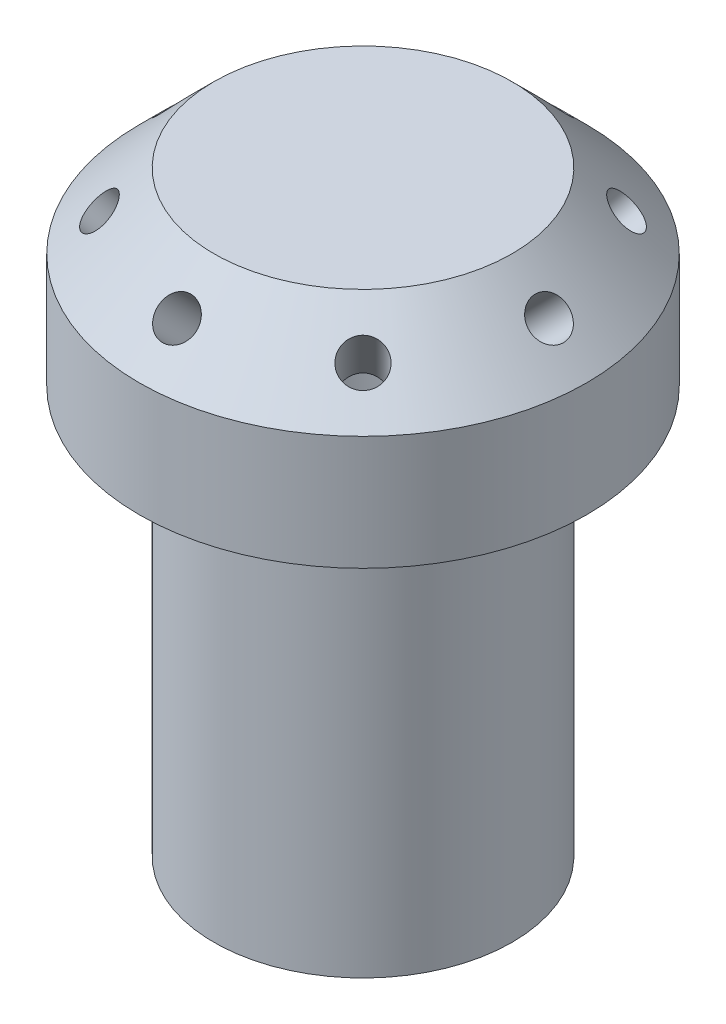
SolidWorks part; units mm, degrees
ref_plane "Front Plane" through (0, 0, 0) normal (0, 0, 1) x (1, 0, 0)
ref_plane "Top Plane" through (0, 0, 0) normal (0, 1, 0) x (1, 0, 0)
ref_plane "Right Plane" through (0, 0, 0) normal (1, 0, 0) x (0, 0, -1)
sketch "Sketch1" plane through (0, 0, 0) normal (0, 0, 1) x (1, 0, 0)
  line L0 (0, 0) -> (0, 93.2125) construction
  line L1 (0, 76.2) -> (19.05, 76.2)
  line L2 (19.05, 76.2) -> (28.575, 66.675)
  line L3 (28.575, 66.675) -> (28.575, 52.07)
  line L4 (28.575, 52.07) -> (19.05, 52.07)
  line L5 (19.05, 52.07) -> (19.05, 0)
  line L6 (19.05, 0) -> (12.7, 0)
  line L8 (12.7, 0) -> (12.7, 48.895)
  line L9 (0, 76.2) -> (0, 61.595)
  arc A0 (12.7, 48.895) -> (0, 61.595) centre (0, 48.895) ccw
  dimension "D1" = 19.05
  dimension "D4" = 14.605
  dimension "D5" = 52.07
  dimension "D7" = 48.895
revolve "Revolve1" add sketch "Sketch1" angle 360 about L0
ref_plane "Plane1" through (47.625, 47.625, 0) normal (-0.7071, -0.7071, 0) x (0, 0, 1)
sketch "Sketch2" plane through (47.625, 47.625, 0) normal (-0.7071, -0.7071, 0) x (0, 0, 1)
  line L0 (0, 40.4112) -> (0, 26.9408) construction
  circle A0 centre (0, 33.676) radius 2.54
  ellipse E0 centre (0, 53.8815) end of major axis (-19.05, 53.8815) minor radius 13.4704 construction
  ellipse E1 centre (0, 47.1463) end of major axis (-28.575, 47.1463) minor radius 20.2056 construction
  point P17 (0, 35.1334)
  dimension "D1" = 5.08
extrude "Cut-Extrude1" cut sketch "Sketch2" along normal up to next
pattern_circular "CirPattern1" count 8 over 360 about axis through (0, 0, 0) along (0, -1, 0) of "Cut-Extrude1"
